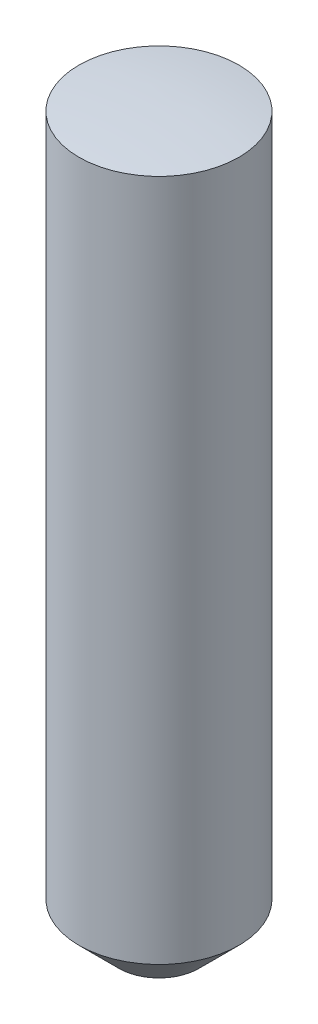
SolidWorks part; units mm, degrees
ref_plane "Front Plane" through (0, 0, 0) normal (0, 0, 1) x (1, 0, 0)
ref_plane "Top Plane" through (0, 0, 0) normal (0, 1, 0) x (1, 0, 0)
ref_plane "Right Plane" through (0, 0, 0) normal (1, 0, 0) x (0, 0, -1)
sketch "Sketch1" plane through (0, 0, 0) normal (0, 1, 0) x (1, 0, 0)
  circle A0 centre (0, 0) radius 1
  dimension "D1" = 2
extrude "Boss-Extrude 9.10mm" add sketch "Sketch1" against normal blind 9.1
chamfer "0.5 x 45 deg" distance 0.5 angle 45 1 edges at (0, -9.1, 1)
sketch "Sketch2" plane through (0, 0, 0) normal (0, 0, 1) x (1, 0, 0)
  line L0 (0, 0) -> (0, 2) construction
  line L1 (0, 2) -> (-2, 2)
  line L2 (-2, 2) -> (-2, -0.254)
  line L3 (0, 0) -> (0, 2)
  arc A0 (0, 0) -> (-2, -0.254) centre (0, -8) ccw
  dimension "D3" = 8
  dimension "D1" = 2
  dimension "D2" = 2
revolve "SR8" cut sketch "Sketch2" angle 360 about L0
